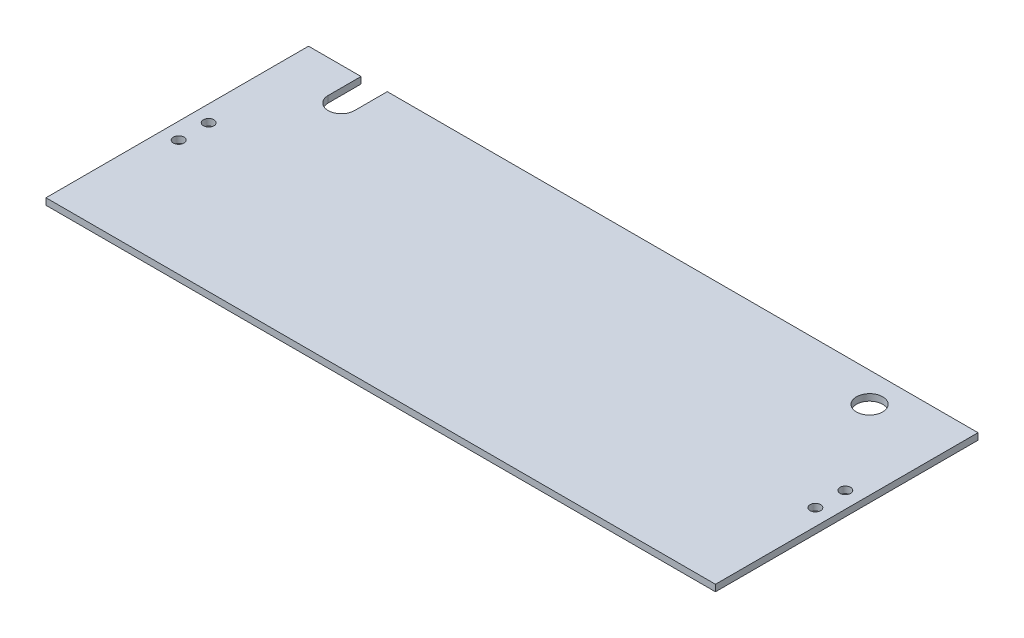
SolidWorks part; units mm, degrees
material "6061-T6 (SS)"
ref_plane "Front Plane" through (0, 0, 0) normal (0, 0, 1) x (1, 0, 0)
ref_plane "Top Plane" through (0, 0, 0) normal (0, 1, 0) x (1, 0, 0)
ref_plane "Right Plane" through (0, 0, 0) normal (1, 0, 0) x (0, 0, -1)
sketch "Sketch1" plane through (0, 0, 0) normal (0, 1, 0) x (1, 0, 0)
  line L1 (0, 0) -> (323.85, 0)
  line L2 (0, 0) -> (0, 127)
  line L3 (0, 127) -> (323.85, 127)
  line L4 (323.85, 0) -> (323.85, 127)
  dimension "D1" = 127
  dimension "D2" = 323.85
extrude "Boss-Extrude1" add sketch "Sketch1" along normal blind 3.175
sketch "Sketch2" plane through (0, 3.175, 0) normal (0, 1, 0) x (1, 0, 0)
  line L0 (31.75, 109.4591) -> (31.75, 111.125) construction
  line L1 (25.4, 111.125) -> (25.4, 127)
  line L3 (25.4, 127) -> (38.1, 127)
  line L4 (38.1, 127) -> (38.1, 111.125)
  line L5 (0, 127) -> (0, 0) construction
  circle A0 centre (31.75, 111.125) radius 6.35
  ellipse E0 centre (31.466, 102.3909) end of major axis (21.466, 102.3909) minor radius 7.0711 construction
  dimension "D1" = 12.7
  dimension "D3" = 31.75
  dimension "D2" = 15.875
extrude "Cut-Extrude1" cut sketch "Sketch2" against normal through all
sketch "Sketch3" plane through (0, -53.975, 0) normal (0, -1, 0) x (-1, 0, 0)
  circle A0 centre (-285.75, 112.649) radius 6.35
extrude "Cut-Extrude2" cut sketch "Sketch3" against normal through all
hole_wizard "#10 Clearance Hole1" positions "Sketch5" profile "Sketch4" hole size "#10" standard "ANSI Inch" end condition through all
sketch "Sketch5" plane through (0, 3.175, 0) normal (0, 1, 0) x (1, 0, 0)
  point P0 (315.9125, 56.25)
  point P3 (315.9125, 70.75)
  point P6 (7.9375, 56.25)
  point P9 (7.9375, 70.75)
sketch "Sketch4" plane through (315.9125, 3.175, -56.25) normal (1, 0, 0) x (0, 0, 1)
  line L0 (0, 0) -> (0, 3.175)
  line L1 (0, 3.175) -> (2.5527, 3.175)
  line L2 (2.5527, 3.175) -> (2.5527, 0)
  line L5 (2.5527, 0) -> (0, 0)
  line L11 (0, -6.35) -> (0, 107.95) construction
  dimension "Thru Hole Dia." = 5.1054
  dimension "Thru Hole Depth" = 3.175
